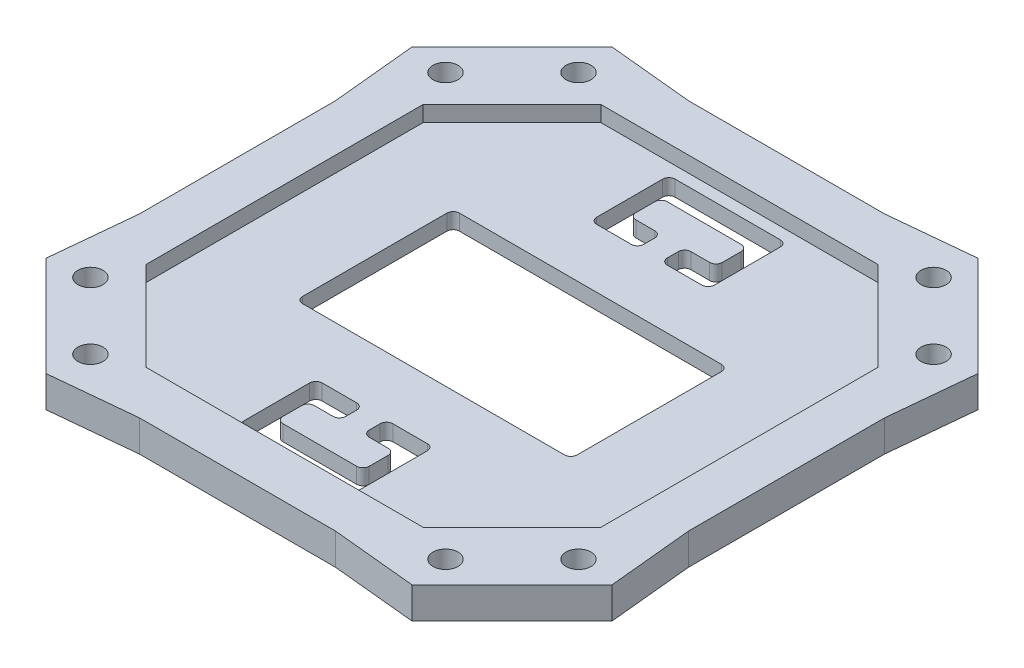
SolidWorks part; units mm, degrees
ref_plane "Front Plane" through (0, 0, 0) normal (0, 0, 1) x (1, 0, 0)
ref_plane "Top Plane" through (0, 0, 0) normal (0, 1, 0) x (1, 0, 0)
ref_plane "Right Plane" through (0, 0, 0) normal (1, 0, 0) x (0, 0, -1)
sketch "Sketch1" plane through (0, 0, 0) normal (0, 1, 0) x (1, 0, 0)
  line L0 (-12.5, 0) -> (12.5, 0)
  line L1 (12.5, 0) -> (23.338, 1.0627)
  line L2 (23.338, 1.0627) -> (36.0659, -11.6652)
  line L3 (36.0659, -11.6652) -> (35.0033, -22.5033)
  line L4 (35.0033, -22.5033) -> (35.0033, -47.5033)
  line L5 (0, 0) -> (0, -59.9756) construction
  line L6 (35.0033, -35.0033) -> (-52.1457, -35.0033) construction
  line L7 (-35.0033, -22.5033) -> (-35.0033, -47.5033)
  line L8 (-36.0659, -11.6652) -> (-35.0033, -22.5033)
  line L9 (-23.338, 1.0627) -> (-36.0659, -11.6652)
  line L10 (-12.5, 0) -> (-23.338, 1.0627)
  line L11 (0, -70.0065) -> (0, -10.0309) construction
  line L12 (-12.5, -70.0065) -> (-23.338, -71.0692)
  line L13 (-23.338, -71.0692) -> (-36.0659, -58.3413)
  line L14 (-36.0659, -58.3413) -> (-35.0033, -47.5033)
  line L15 (36.0659, -58.3413) -> (35.0033, -47.5033)
  line L16 (23.338, -71.0692) -> (36.0659, -58.3413)
  line L17 (12.5, -70.0065) -> (23.338, -71.0692)
  line L18 (-12.5, -70.0065) -> (12.5, -70.0065)
  point P17 (-35.0033, -35.0033)
  dimension "D1" = 12.5
  dimension "D2" = 10.89
  dimension "D3" = 5.6
  dimension "D4" = 18
  dimension "D5" = 50.6
  dimension "D6" = 50.6
  dimension "D7" = 10.89
  dimension "D8" = 12.5
extrude "Boss-Extrude1" add sketch "Sketch1" along normal blind 4
sketch "Sketch2" plane through (0, 4, 0) normal (0, 1, 0) x (1, 0, 0)
  line L0 (0, 0) -> (0, -70.0065) construction
  line L1 (-12.5, -70.0065) -> (12.5, -70.0065) construction
  line L2 (-35.0033, -35.0033) -> (35.0033, -35.0033) construction
  line L3 (-35.0033, -22.5033) -> (-35.0033, -47.5033) construction
  line L4 (35.0033, -47.5033) -> (35.0033, -22.5033) construction
  circle A0 centre (22.63, -3.8933) radius 1.6
  circle A1 centre (31.11, -12.3733) radius 1.6
  circle A2 centre (-31.11, -12.3733) radius 1.6
  circle A3 centre (-22.63, -3.8933) radius 1.6
  circle A4 centre (31.11, -57.6333) radius 1.6
  circle A5 centre (22.63, -66.1133) radius 1.6
  circle A6 centre (-22.63, -66.1133) radius 1.6
  circle A7 centre (-31.11, -57.6333) radius 1.6
  dimension "D1" = 3.2
  dimension "D2" = 3.2
  dimension "D3" = 22.63
  dimension "D4" = 31.11
  dimension "D5" = 31.11
  dimension "D6" = 22.63
extrude "Cut-Extrude1" cut sketch "Sketch2" against normal through all
sketch "Sketch3" plane through (0, 4, 0) normal (0, 1, 0) x (1, 0, 0)
  line L0 (-17.6728, -6) -> (17.6728, -6)
  line L1 (-29.0033, -17.3305) -> (-29.0033, -52.6761)
  line L3 (-17.6728, -64.0065) -> (17.6728, -64.0065)
  line L4 (12.5, 0) -> (-12.5, 0) construction
  line L5 (-35.0033, -22.5033) -> (-35.0033, -47.5033) construction
  line L6 (-12.5, -70.0065) -> (12.5, -70.0065) construction
  line L7 (35.0033, -47.5033) -> (35.0033, -22.5033) construction
  line L8 (-17.6728, -6) -> (-29.0033, -17.3305)
  line L9 (-23.338, 1.0627) -> (-36.0659, -11.6652) construction
  line L11 (0, 0) -> (0, -70.0065) construction
  line L12 (-35.0033, -35.0033) -> (35.0033, -35.0033) construction
  line L13 (17.6728, -6) -> (29.0033, -17.3305)
  line L14 (17.6728, -64.0065) -> (29.0033, -52.6761)
  line L15 (-17.6728, -64.0065) -> (-29.0033, -52.6761)
  line L16 (29.0033, -17.3305) -> (29.0033, -52.6761)
  dimension "D1" = 6
  dimension "D2" = 6
  dimension "D5" = 9
extrude "Cut-Extrude2" cut sketch "Sketch3" against normal blind 2
sketch "Sketch4" plane through (0, 2, 0) normal (0, 1, 0) x (1, 0, 0)
  line L1 (-16.7, -45.0033) -> (16.7, -45.0033)
  line L2 (-17.5, -44.2033) -> (-17.5, -25.8033)
  line L3 (-16.7, -25.0033) -> (16.7, -25.0033)
  line L4 (17.5, -44.2033) -> (17.5, -25.8033)
  line L5 (-17.5, -45.0033) -> (17.5, -25.0033) construction
  line L6 (-17.5, -25.0033) -> (17.5, -45.0033) construction
  line L7 (-29.0033, -17.3305) -> (-29.0033, -52.6761) construction
  line L8 (-1.5, -16.7033) -> (-1.5, -15.3033)
  line L9 (-6.7, -17.5033) -> (-2.3, -17.5033)
  line L10 (-7.5, -16.7033) -> (-7.5, -8.3033)
  line L11 (-6.7, -7.5033) -> (6.7, -7.5033)
  line L12 (7.5, -16.7033) -> (7.5, -8.3033)
  line L13 (-7.5, -17.5033) -> (7.5, -7.5033) construction
  line L14 (-7.5, -7.5033) -> (7.5, -17.5033) construction
  line L15 (-4.7, -14.5033) -> (-2.3, -14.5033)
  line L16 (-5.5, -13.7033) -> (-5.5, -11.3033)
  line L17 (-4.7, -10.5033) -> (4.7, -10.5033)
  line L18 (5.5, -13.7033) -> (5.5, -11.3033)
  line L19 (-5.5, -14.5033) -> (5.5, -10.5033) construction
  line L20 (-5.5, -10.5033) -> (5.5, -14.5033) construction
  line L21 (1.5, -16.7033) -> (1.5, -15.3033)
  line L22 (2.3, -17.5033) -> (6.7, -17.5033)
  line L23 (2.3, -14.5033) -> (4.7, -14.5033)
  line L24 (-29.0033, -35.0033) -> (29.0033, -35.0033) construction
  line L25 (-29.0033, -17.3305) -> (-29.0033, -52.6761) construction
  line L26 (29.0033, -52.6761) -> (29.0033, -17.3305) construction
  line L27 (-5.5, -56.3033) -> (-5.5, -58.7033)
  line L28 (-4.7, -59.5033) -> (4.7, -59.5033)
  line L29 (5.5, -56.3033) -> (5.5, -58.7033)
  line L30 (2.3, -55.5033) -> (4.7, -55.5033)
  line L31 (1.5, -53.3033) -> (1.5, -54.7033)
  line L32 (2.3, -52.5033) -> (6.7, -52.5033)
  line L33 (7.5, -53.3033) -> (7.5, -61.7033)
  line L34 (-6.7, -62.5033) -> (6.7, -62.5033)
  line L35 (-7.5, -53.3033) -> (-7.5, -61.7033)
  line L36 (-6.7, -52.5033) -> (-2.3, -52.5033)
  line L37 (-1.5, -53.3033) -> (-1.5, -54.7033)
  line L38 (-4.7, -55.5033) -> (-2.3, -55.5033)
  arc A0 (2.3, -17.5033) -> (1.5, -16.7033) centre (2.3, -16.7033) cw
  arc A1 (-1.5, -16.7033) -> (-2.3, -17.5033) centre (-2.3, -16.7033) cw
  arc A2 (-6.7, -17.5033) -> (-7.5, -16.7033) centre (-6.7, -16.7033) cw
  arc A3 (-4.7, -14.5033) -> (-5.5, -13.7033) centre (-4.7, -13.7033) cw
  arc A4 (-1.5, -15.3033) -> (-2.3, -14.5033) centre (-2.3, -15.3033) ccw
  arc A5 (1.5, -15.3033) -> (2.3, -14.5033) centre (2.3, -15.3033) cw
  arc A6 (4.7, -14.5033) -> (5.5, -13.7033) centre (4.7, -13.7033) ccw
  arc A7 (4.7, -10.5033) -> (5.5, -11.3033) centre (4.7, -11.3033) cw
  arc A8 (-5.5, -11.3033) -> (-4.7, -10.5033) centre (-4.7, -11.3033) cw
  arc A9 (6.7, -17.5033) -> (7.5, -16.7033) centre (6.7, -16.7033) ccw
  arc A10 (6.7, -7.5033) -> (7.5, -8.3033) centre (6.7, -8.3033) cw
  arc A11 (-7.5, -8.3033) -> (-6.7, -7.5033) centre (-6.7, -8.3033) cw
  arc A12 (-5.5, -58.7033) -> (-4.7, -59.5033) centre (-4.7, -58.7033) ccw
  arc A13 (4.7, -59.5033) -> (5.5, -58.7033) centre (4.7, -58.7033) ccw
  arc A14 (4.7, -55.5033) -> (5.5, -56.3033) centre (4.7, -56.3033) cw
  arc A15 (1.5, -54.7033) -> (2.3, -55.5033) centre (2.3, -54.7033) ccw
  arc A16 (2.3, -52.5033) -> (1.5, -53.3033) centre (2.3, -53.3033) ccw
  arc A17 (6.7, -52.5033) -> (7.5, -53.3033) centre (6.7, -53.3033) cw
  arc A18 (6.7, -62.5033) -> (7.5, -61.7033) centre (6.7, -61.7033) ccw
  arc A19 (-7.5, -61.7033) -> (-6.7, -62.5033) centre (-6.7, -61.7033) ccw
  arc A20 (-6.7, -52.5033) -> (-7.5, -53.3033) centre (-6.7, -53.3033) ccw
  arc A21 (-1.5, -53.3033) -> (-2.3, -52.5033) centre (-2.3, -53.3033) ccw
  arc A22 (-4.7, -55.5033) -> (-5.5, -56.3033) centre (-4.7, -56.3033) ccw
  arc A23 (-1.5, -54.7033) -> (-2.3, -55.5033) centre (-2.3, -54.7033) cw
  arc A24 (-17.5, -25.8033) -> (-16.7, -25.0033) centre (-16.7, -25.8033) cw
  arc A25 (16.7, -25.0033) -> (17.5, -25.8033) centre (16.7, -25.8033) cw
  arc A26 (16.7, -45.0033) -> (17.5, -44.2033) centre (16.7, -44.2033) ccw
  arc A27 (-16.7, -45.0033) -> (-17.5, -44.2033) centre (-16.7, -44.2033) cw
  point P0 (0, -35.0033)
  point P5 (-1.5, -17.5033)
  point P7 (0, -12.5033)
  point P8 (0, -12.5033)
  point P12 (-29.0033, -35.0033)
  point P20 (1.5, -17.5033)
  point P27 (1.5, -17.5033)
  point P30 (-1.5, -17.5033)
  point P41 (1.5, -14.5033)
  dimension "D9" = 0.8
  dimension "D11" = 0.8
  dimension "D1" = 20
  dimension "D2" = 35
  dimension "D3" = 10
  dimension "D4" = 15
  dimension "D5" = 3
  dimension "D6" = 2
  dimension "D7" = 6
  dimension "D8" = 6
  dimension "D10" = 17.5
extrude "Cut-Extrude3" cut sketch "Sketch4" against normal through all
